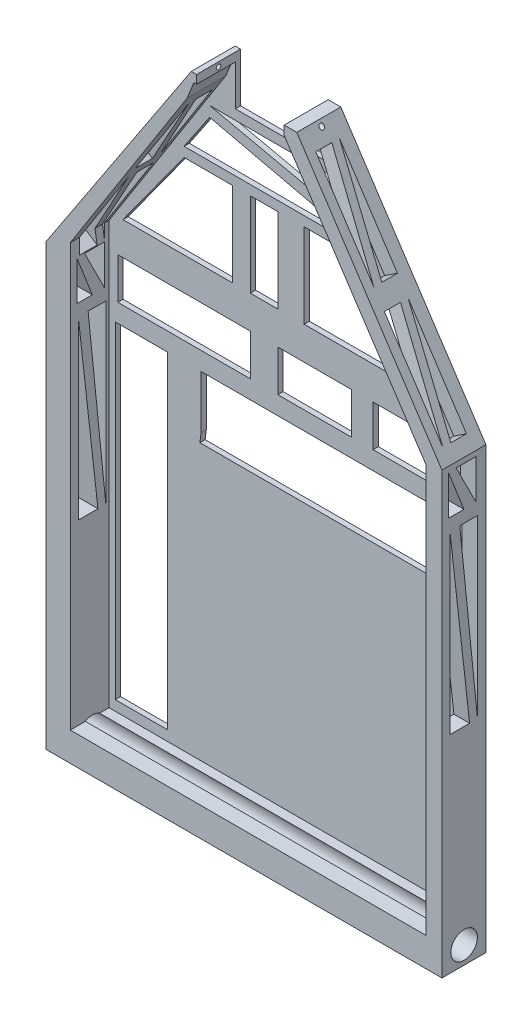
SolidWorks part; units mm, degrees
ref_plane "Front Plane" through (0, 0, 0) normal (0, 0, 1) x (1, 0, 0)
ref_plane "Top Plane" through (0, 0, 0) normal (0, 1, 0) x (1, 0, 0)
ref_plane "Right Plane" through (0, 0, 0) normal (1, 0, 0) x (0, 0, -1)
sketch "Sketch1" plane through (0, 0, 0) normal (0, 0, 1) x (1, 0, 0)
  line L0 (0, 0) -> (57.15, 0)
  line L1 (57.15, 0) -> (57.15, 63.5)
  line L4 (0, 63.5) -> (0, 0)
  line L5 (0, 63.5) -> (20.955, 95.25)
  line L6 (20.955, 95.25) -> (28.575, 95.25)
  line L7 (28.575, 95.25) -> (36.195, 95.25)
  line L8 (36.195, 95.25) -> (57.15, 63.5)
  dimension "D1" = 63.5
  dimension "D2" = 57.15
  dimension "D3" = 63.5
extrude "Boss-Extrude2" add sketch "Sketch1" along normal blind 6.35
sketch "Sketch2" plane through (0, 0, 6.35) normal (0, 0, 1) x (1, 0, 0)
  line L0 (57.15, 0) -> (19.05, 0) construction
  line L1 (20.364, 91.6165) -> (21.329, 94.0167)
  line L2 (0, 0) -> (57.15, 0) construction
  line L3 (21.329, 94.0167) -> (34.3391, 94.0167)
  line L4 (57.15, 0) -> (57.15, 38.1) construction
  line L5 (57.15, 0) -> (57.15, 63.5) construction
  line L6 (34.3391, 94.0167) -> (54.8827, 62.9615)
  line L7 (54.8827, 62.9615) -> (54.8827, 4.1734)
  line L8 (54.8827, 4.1734) -> (3.4964, 4.1734)
  line L9 (3.4964, 4.1734) -> (3.4964, 65.1099)
  line L10 (3.4964, 65.1099) -> (20.364, 91.6165)
  dimension "D1" = 38.1
extrude "Cut-Extrude1" cut sketch "Sketch2" against normal blind 5.588
sketch "Sketch4" plane through (57.15, 0, 0) normal (1, 0, 0) x (0, 0, -1)
  line L0 (-5.3749, 3.8979) -> (-2.9036, 3.8979)
  line L1 (-2.9036, 3.8979) -> (-5.3749, 27.5893)
  line L2 (-5.3749, 27.5893) -> (-5.3749, 3.8979)
  line L3 (-4.1393, 27.5893) -> (-1.6627, 27.5893)
  line L4 (-1.6627, 27.5893) -> (-1.6627, 3.8979)
  line L5 (-1.6627, 3.8979) -> (-4.1393, 27.5893)
sketch "Sketch5" plane through (57.15, 0, 0) normal (1, 0, 0) x (0, 0, -1)
  line L0 (-5.198, 29.8499) -> (-2.3569, 29.8499)
  line L1 (-5.198, 29.8499) -> (-5.198, 55.2607)
  line L2 (-5.198, 55.2607) -> (-2.3569, 29.8499)
  line L3 (-1.2163, 29.8499) -> (-1.2163, 55.2607)
  line L4 (-1.2163, 55.2607) -> (-3.7774, 55.2607)
  line L5 (-3.7774, 55.2607) -> (-1.2163, 29.8499)
extrude "Cut-Extrude3" cut sketch "Sketch5" against normal through all
sketch "Sketch6" plane through (57.15, 0, 0) normal (1, 0, 0) x (0, 0, -1)
  line L0 (-5.413, 57.0031) -> (-3.1708, 57.0031)
  line L1 (-3.1708, 57.0031) -> (-5.413, 62.735)
  line L2 (-5.413, 62.735) -> (-5.413, 57.0031)
  line L3 (-4.2919, 62.735) -> (-1.4123, 62.735)
  line L4 (-1.4123, 62.735) -> (-1.4123, 57.0031)
  line L5 (-1.4123, 57.0031) -> (-4.2919, 62.735)
extrude "Cut-Extrude4" cut sketch "Sketch6" against normal through all
sketch "Sketch7" plane through (69.0025, 45.5417, 0) normal (0.8346, 0.5508, 0) x (0, 0, -1)
  line L0 (-5.1251, 23.5171) -> (-5.1251, 38.8188)
  line L1 (-5.1251, 38.8188) -> (-2.8048, 38.8188)
  line L2 (-2.8048, 38.8188) -> (-5.1251, 23.5171)
  line L3 (-3.9649, 23.5171) -> (-1.7101, 23.5171)
  line L4 (-1.7101, 23.5171) -> (-1.7101, 38.8188)
  line L5 (-1.7101, 38.8188) -> (-3.9649, 23.5171)
  line L6 (-5.1251, 41.6008) -> (-5.1251, 56.8139)
  line L7 (-5.1251, 56.8139) -> (-2.8048, 56.8139)
  line L8 (-2.8048, 56.8139) -> (-5.1251, 41.6008)
  line L9 (-3.9649, 41.6008) -> (-1.7101, 41.6008)
  line L10 (-1.7101, 41.6008) -> (-1.7101, 56.8139)
  line L11 (-1.7101, 56.8139) -> (-3.9649, 41.6008)
extrude "Cut-Extrude5" cut sketch "Sketch7" against normal blind 5.588
sketch "Sketch8" plane through (-29.1934, 19.2676, 0) normal (-0.8346, 0.5508, 0) x (0, 0, 1)
  line L0 (5.0147, 54.4013) -> (2.4737, 54.4013)
  line L1 (2.4737, 54.4013) -> (5.0147, 69.3387)
  line L2 (5.0147, 69.3387) -> (5.0147, 54.4013)
  line L3 (1.4019, 54.4013) -> (1.4019, 69.3387)
  line L4 (1.4019, 69.3387) -> (3.7442, 69.3387)
  line L5 (3.7442, 69.3387) -> (1.4019, 54.4013)
  line L6 (5.0147, 71.2978) -> (2.5731, 71.2978)
  line L7 (2.5731, 71.2978) -> (4.7552, 85.2143)
  line L8 (4.7552, 85.2143) -> (5.0147, 71.2978)
  line L9 (1.4019, 71.2978) -> (1.4019, 85.2143)
  line L10 (1.4019, 85.2143) -> (3.7939, 85.2143)
  line L11 (3.7939, 85.2143) -> (1.4019, 71.2978)
extrude "Cut-Extrude6" cut sketch "Sketch8" against normal blind 5.588
sketch "Sketch9" plane through (0, 95.25, 0) normal (0, 1, 0) x (1, 0, 0)
  line L0 (25.5286, -6.35) -> (25.5286, 0)
  line L1 (36.195, -6.35) -> (20.955, -6.35) construction
  line L2 (36.195, 0) -> (20.955, 0) construction
  line L3 (31.3635, -6.35) -> (31.3635, 0)
  line L4 (25.5286, 0) -> (31.3635, 0)
  line L5 (25.5286, -6.35) -> (31.3635, -6.35)
extrude "Cut-Extrude7" cut sketch "Sketch9" against normal blind 5.588
sketch "Sketch10" plane through (25.5286, 0, 0) normal (1, 0, 0) x (0, 0, -1)
  line L0 (-3.175, 95.25) -> (-3.1452, 94.0167) construction
  line L1 (0, 95.25) -> (-6.35, 95.25) construction
  line L2 (-0.762, 94.0167) -> (-6.35, 94.0167) construction
  line L3 (0, 95.25) -> (-3.175, 95.25) construction
  circle A0 centre (-3.1601, 94.6333) radius 0.508
  dimension "D2" = 1.016
sketch "Sketch13" plane through (0, 0, 0) normal (-1, 0, 0) x (0, 0, 1)
  circle A0 centre (3.178, 1.9875) radius 1.5163
sketch "Sketch14" plane through (0, 0, 0.762) normal (0, 0, 1) x (1, 0, 0)
  line L0 (54.8827, 4.1734) -> (16.7827, 4.1734) construction
  line L1 (3.4964, 4.1734) -> (54.8827, 4.1734) construction
  line L2 (16.7827, 4.1734) -> (16.7827, 42.2734) construction
  line L3 (16.7827, 42.2734) -> (54.8827, 42.2734) construction
  line L4 (54.8827, 4.1734) -> (54.8827, 62.9615) construction
  line L5 (16.7827, 45.2374) -> (16.7827, 52.8574)
  line L6 (16.7827, 52.8574) -> (52.1303, 52.8574)
  line L7 (52.1303, 52.8574) -> (52.1303, 45.2374)
  line L8 (52.1303, 45.2374) -> (16.7827, 45.2374)
  line L9 (11.9273, 52.8574) -> (11.9273, 5.6358)
  line L10 (11.9273, 5.6358) -> (4.405, 5.6358)
  line L11 (4.405, 5.6358) -> (4.405, 52.8574)
  line L12 (4.405, 52.8574) -> (11.9273, 52.8574)
  dimension "D1" = 38.1
  dimension "D2" = 38.1
extrude "Cut-Extrude15" cut sketch "Sketch14" against normal through all
sketch "Sketch15" plane through (0, 0, 0.762) normal (0, 0, 1) x (1, 0, 0)
  line L0 (54.8827, 4.1734) -> (54.8827, 42.2734) construction
  line L1 (54.8827, 4.1734) -> (54.8827, 62.9615) construction
  line L2 (54.8827, 42.2734) -> (16.7827, 42.2734) construction
  line L3 (16.7827, 42.2734) -> (16.7827, 4.1734) construction
  line L4 (3.4964, 4.1734) -> (54.8827, 4.1734) construction
  line L5 (16.7827, 4.1734) -> (54.8827, 4.1734) construction
  line L6 (16.7827, 42.2734) -> (54.8827, 42.2734)
  line L7 (54.8827, 42.2734) -> (54.8827, 4.1734)
  line L8 (54.8827, 4.1734) -> (16.7827, 4.1734)
  line L9 (16.7827, 4.1734) -> (16.7827, 42.2734)
  line L10 (16.7827, 45.2374) -> (16.6219, 43.8652)
  line L11 (16.6219, 43.8652) -> (52.1488, 43.8652)
  line L12 (52.1488, 43.8652) -> (52.1303, 45.2374)
  line L13 (16.7827, 45.2374) -> (52.1303, 45.2374) construction
  line M6 (52.1303, 45.2374) -> (16.7827, 45.2374)
extrude "Cut-Extrude16" cut sketch "Sketch15" against normal through all contours L11 L12 L10 M6
sketch "Sketch16" plane through (0, 0, 0.762) normal (0, 0, 1) x (1, 0, 0)
  line L0 (4.7639, 61.4519) -> (4.7639, 55.4937)
  line L1 (4.7639, 55.4937) -> (23.9016, 55.4937)
  line L2 (23.9016, 55.4937) -> (23.9016, 61.4519)
  line L3 (23.9016, 61.4519) -> (4.7639, 61.4519)
  line L4 (27.8589, 61.4519) -> (38.5172, 61.4519)
  line L5 (38.5172, 61.4519) -> (38.5172, 55.4937)
  line L6 (38.5172, 55.4937) -> (27.8589, 55.4937)
  line L7 (27.8589, 55.4937) -> (27.8589, 61.4519)
  line L8 (41.6204, 61.4519) -> (53.021, 61.4519)
  line L9 (53.021, 61.4519) -> (53.021, 55.4937)
  line L10 (53.021, 55.4937) -> (41.6204, 55.4937)
  line L11 (41.6204, 55.4937) -> (41.6204, 61.4519)
  line L12 (49.9891, 66.1997) -> (41.6204, 78.3836)
  line L13 (41.6204, 78.3836) -> (31.6769, 78.3836)
  line L14 (31.6769, 78.3836) -> (31.6769, 66.1997)
  line L15 (31.6769, 66.1997) -> (49.9891, 66.1997)
  line L16 (27.8589, 78.3836) -> (23.9016, 78.3836)
  line L17 (23.9016, 78.3836) -> (23.9016, 66.1997)
  line L18 (23.9016, 66.1997) -> (27.8589, 66.1997)
  line L19 (27.8589, 66.1997) -> (27.8589, 78.3836)
  line L20 (5.5079, 66.1997) -> (14.3328, 78.3836)
  line L21 (14.3328, 78.3836) -> (21.3169, 78.3836)
  line L22 (21.3169, 78.3836) -> (21.3169, 66.1997)
  line L23 (21.3169, 66.1997) -> (5.5079, 66.1997)
  line L24 (18.0222, 85.2509) -> (14.3328, 79.7836)
  line L25 (14.3328, 79.7836) -> (41.6204, 79.7836)
  line L26 (41.6204, 79.7836) -> (18.0222, 85.2509)
  line L27 (18.0222, 86.7339) -> (37.5771, 86.7339)
  line L28 (37.5771, 86.7339) -> (41.6204, 81.5146)
  line L29 (41.6204, 81.5146) -> (18.0222, 86.7339)
extrude "Cut-Extrude18" cut sketch "Sketch16" against normal through all
sketch "Sketch24" plane through (0, 0, 0) normal (0, 0, -1) x (-1, 0, 0)
  line L0 (-25.5286, 95.25) -> (-25.5286, 89.662)
  line L2 (-25.5286, 89.662) -> (-21.724, 89.662)
  line L3 (-21.724, 89.662) -> (-21.724, 95.25)
  line L5 (-25.5286, 95.25) -> (-20.955, 95.25) construction
  line L6 (-21.724, 95.25) -> (-25.5286, 95.25)
extrude "Cut-Extrude24" cut sketch "Sketch24" against normal through all
sketch "Sketch25" plane through (0, 0, 0) normal (0, 0, -1) x (-1, 0, 0)
  line L0 (-21.724, 89.662) -> (-21.724, 88.1654)
  line L1 (-21.724, 88.1654) -> (-34.3777, 88.1654)
  line L2 (-34.3777, 88.1654) -> (-34.3777, 89.662)
  line L3 (-34.3777, 89.662) -> (-31.3635, 89.662)
  line L4 (-21.724, 89.662) -> (-31.3635, 89.662)
extrude "Cut-Extrude25" cut sketch "Sketch25" against normal blind 11.684
sketch "Sketch26" plane through (0, 0, 0) normal (0, 0, -1) x (-1, 0, 0)
  line L0 (-34.3777, 89.662) -> (-34.3777, 95.25)
  line L1 (-36.195, 95.25) -> (-31.3635, 95.25) construction
  line L2 (-34.3777, 95.25) -> (-31.3635, 95.25)
  line L3 (-31.3635, 95.25) -> (-31.3635, 89.662)
  line L4 (-31.3635, 89.662) -> (-34.3777, 89.662)
extrude "Cut-Extrude26" cut sketch "Sketch26" against normal blind 11.684
sketch "Sketch28" plane through (34.3777, 0, 0) normal (-1, 0, 0) x (0, 0, 1)
  line L0 (6.35, 94.6042) -> (0, 94.6042) construction
  line L1 (6.35, 93.9584) -> (6.35, 95.25) construction
  line L2 (0, 95.25) -> (0, 88.1654) construction
  circle A0 centre (3.175, 94.6042) radius 0.3334
extrude "Cut-Extrude27" cut sketch "Sketch28" against normal through all and the other way through all
sketch "Sketch29" plane through (57.15, 0, 0) normal (1, 0, 0) x (0, 0, -1)
  circle A0 centre (-3.1517, 2.5459) radius 1.9242
extrude "Cut-Extrude28" cut sketch "Sketch29" against normal through all
sketch "Sketch30" plane through (0, 0, 0.762) normal (0, 0, 1) x (1, 0, 0)
  line L0 (24.2085, 88.1654) -> (31.0713, 88.1654)
  line L2 (34.3777, 88.1654) -> (21.724, 88.1654) construction
  line L4 (31.0713, 88.1654) -> (31.0713, 99.6294)
  line L5 (31.0713, 99.6294) -> (24.2085, 99.6294)
  line L6 (24.2085, 99.6294) -> (24.2085, 88.1654)
  line L17 (54.8827, 62.9615) -> (34.3777, 93.9584)
  line L18 (34.3777, 93.9584) -> (34.3777, 88.1654)
  line L19 (34.3777, 88.1654) -> (21.724, 88.1654)
  line L20 (21.724, 88.1654) -> (21.724, 94.0167)
  line L21 (21.724, 94.0167) -> (21.329, 94.0167)
  line L22 (21.329, 94.0167) -> (20.364, 91.6165)
  line L23 (20.364, 91.6165) -> (3.4964, 65.1099)
  line L24 (3.4964, 65.1099) -> (3.4964, 4.1734)
  line L25 (3.4964, 4.1734) -> (54.8827, 4.1734)
  line L26 (54.8827, 4.1734) -> (54.8827, 62.9615)
  line L27 (54.8827, 62.9615) -> (34.3777, 93.9584)
  line L28 (34.3777, 93.9584) -> (34.3777, 88.1654)
  line L30 (21.724, 88.1654) -> (21.724, 94.0167)
  line L31 (21.724, 94.0167) -> (21.329, 94.0167)
  line L32 (21.329, 94.0167) -> (20.364, 91.6165)
  line L33 (20.364, 91.6165) -> (3.4964, 65.1099)
  line L34 (3.4964, 65.1099) -> (3.4964, 4.1734)
  line L35 (3.4964, 4.1734) -> (54.8827, 4.1734)
  line L36 (54.8827, 4.1734) -> (54.8827, 62.9615)
  dimension "D1" = 0
sketch "Sketch31" plane through (0, 0, 0.762) normal (0, 0, 1) x (1, 0, 0)
  line L0 (21.724, 88.1654) -> (34.3777, 88.1654) construction
  line L1 (34.3777, 88.1654) -> (34.3777, 105.9454) construction
  line L2 (34.3777, 105.9454) -> (21.724, 105.9454) construction
  line L3 (21.724, 105.9454) -> (21.724, 88.1654) construction
  line L4 (21.724, 105.9454) -> (34.3777, 105.9454)
  line L5 (34.3777, 105.9454) -> (34.3777, 88.1654)
  line L6 (34.3777, 88.1654) -> (21.724, 88.1654)
  line L7 (21.724, 88.1654) -> (21.724, 105.9454)
  dimension "D1" = 17.78
